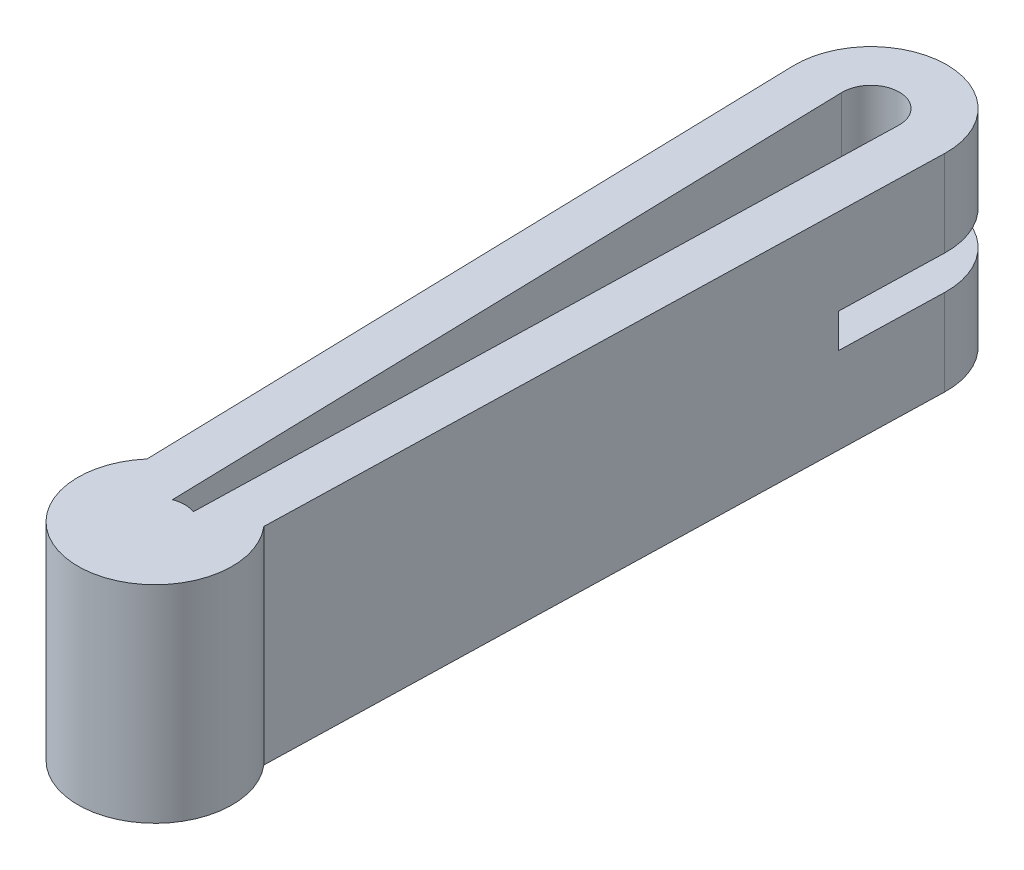
SolidWorks part; units mm, degrees
ref_plane "Front Plane" through (0, 0, 0) normal (0, 0, 1) x (1, 0, 0)
ref_plane "Top Plane" through (0, 0, 0) normal (0, 1, 0) x (1, 0, 0)
ref_plane "Right Plane" through (0, 0, 0) normal (1, 0, 0) x (0, 0, -1)
sketch "Sketch1" plane through (0, 0, 0) normal (0, 1, 0) x (1, 0, 0)
  line L0 (-10.1565, -0.266) -> (-7.8286, -89.166)
  line L1 (10.1565, -0.266) -> (7.8286, -89.166)
  line L2 (0, 15.9405) -> (0, -57.1464) construction
  arc A0 (10.1565, -0.266) -> (-10.1565, -0.266) centre (0, 0) ccw
  arc A1 (-7.8286, -89.166) -> (7.8286, -89.166) centre (0, -95.9115) ccw
  point P1 (-7.8286, -89.166)
  dimension "D1" = 20.32
  dimension "D2" = 1.5
  dimension "D3" = 1.5
  dimension "D4" = 88.9
  dimension "D5" = 88.9
extrude "Boss-Extrude1" add sketch "Sketch1" along normal blind 27.686 contours L0 A1 L1 A0
ref_plane "Plane1" through (0, 0, 0.266) normal (0, 0, -1) x (-1, 0, 0)
sketch "Sketch2" plane through (0, 0, 0.266) normal (0, 0, -1) x (-1, 0, 0)
  line L1 (-13.8535, 16.129) -> (16.0684, 16.129)
  line L2 (-13.8535, 16.129) -> (-13.8535, 11.557)
  line L3 (-13.8535, 11.557) -> (16.0684, 11.557)
  line L4 (16.0684, 16.129) -> (16.0684, 11.557)
  line L5 (10.3339, 27.686) -> (-10.3339, 27.686) construction
  dimension "D1" = 4.572
  dimension "D2" = 11.557
extrude "Cut-Extrude1" cut sketch "Sketch2" against normal mid plane 27.686
sketch "Sketch3" plane through (0, 0, 0) normal (0, -1, 0) x (1, 0, 0)
  line L0 (-1.3975, 92.1808) -> (-3.8087, 0.0997)
  line L1 (3.8087, 0.0997) -> (1.3975, 92.1808)
  line L2 (10.1565, 0.266) -> (7.8286, 89.166)
  line L3 (-7.8286, 89.166) -> (-10.1565, 0.266)
  line L4 (10.1565, 0.266) -> (7.8286, 89.166)
  line L5 (-7.8286, 89.166) -> (-10.1565, 0.266)
  arc A0 (-3.8087, 0.0997) -> (3.8087, 0.0997) centre (0, 0) ccw
  arc A2 (-10.1565, 0.266) -> (10.1565, 0.266) centre (0, 0) ccw
  arc A3 (7.8286, 89.166) -> (-7.8286, 89.166) centre (0, 95.9115) ccw
  arc A4 (-10.1565, 0.266) -> (10.1565, 0.266) centre (0, 0) ccw
  arc A5 (7.8286, 89.166) -> (-7.8286, 89.166) centre (0, 95.9115) ccw
  arc A6 (-1.3975, 92.1808) -> (1.3975, 92.1808) centre (0, 95.9115) ccw
  arc A7 (1.3975, 92.1808) -> (-1.3975, 92.1808) centre (0, 95.9115) ccw construction
  dimension "D1" = 0
  dimension "D2" = 6.35
extrude "Cut-Extrude2" cut sketch "Sketch3" against normal blind 27.686 flip side to cut
